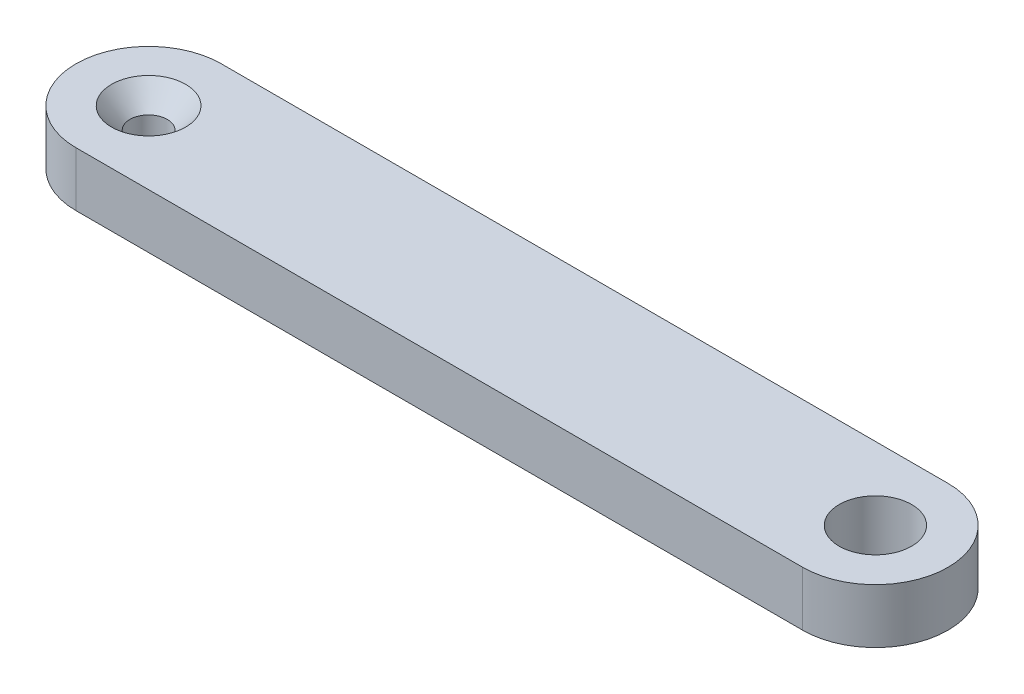
SolidWorks part; units mm, degrees
material "6061-T6 (SS)"
ref_plane "Front Plane" through (0, 0, 0) normal (0, 0, 1) x (1, 0, 0)
ref_plane "Top Plane" through (0, 0, 0) normal (0, 1, 0) x (1, 0, 0)
ref_plane "Right Plane" through (0, 0, 0) normal (1, 0, 0) x (0, 0, -1)
sketch "Sketch1" plane through (0, 0, 0) normal (0, 1, 0) x (1, 0, 0)
  line L0 (-63.5, 0) -> (0, 0) construction
  line L1 (-63.5, 6.35) -> (0, 6.35)
  line L2 (-63.5, -6.35) -> (0, -6.35)
  arc A0 (-63.5, 6.35) -> (-63.5, -6.35) centre (-63.5, 0) ccw
  arc A1 (0, -6.35) -> (0, 6.35) centre (0, 0) ccw
  point P2 (-31.75, 0)
  point P9 (-69.85, 0)
  point P10 (6.35, 0)
  dimension "D2" = 76.2
  dimension "D1" = 12.7
extrude "Boss-Extrude2" add sketch "Sketch1" along normal blind 4.7625
sketch "Sketch2" plane through (0, 4.7625, 0) normal (0, 1, 0) x (1, 0, 0)
  circle A0 centre (0, 0) radius 3.1623
  dimension "D1" = 6.3246
extrude "Cut-Extrude1" cut sketch "Sketch2" against normal through all
hole_wizard "CSK for #4 Flat Head Socket Cap Screw1" positions "Sketch3" profile "Sketch4" countersink size "#4" standard "ANSI Inch" end condition through all
sketch "Sketch3" plane through (0, 4.7625, 0) normal (0, 1, 0) x (1, 0, 0)
  point P0 (-63.5, 0)
sketch "Sketch4" plane through (-63.5, 4.7625, 0) normal (1, 0, 0) x (0, 0, 1)
  line L0 (0, 0) -> (0, 4.7625)
  line L1 (0, 4.7625) -> (1.6319, 4.7625)
  line L2 (1.6319, 4.7625) -> (1.6319, 1.8481)
  line L3 (1.6319, 1.8481) -> (3.2385, 0)
  line L5 (3.2385, 0) -> (0, 0)
  line L6 (-1.632, 1.8481) -> (-3.2385, 0) construction
  line L11 (0, -6.35) -> (0, 107.95) construction
  dimension "Thru Hole Dia." = 3.2639
  dimension "Thru Hole Depth" = 4.7625
  dimension "Near C'Sink Dia." = 6.477
  dimension "Near C'Sink Angle" = 82
